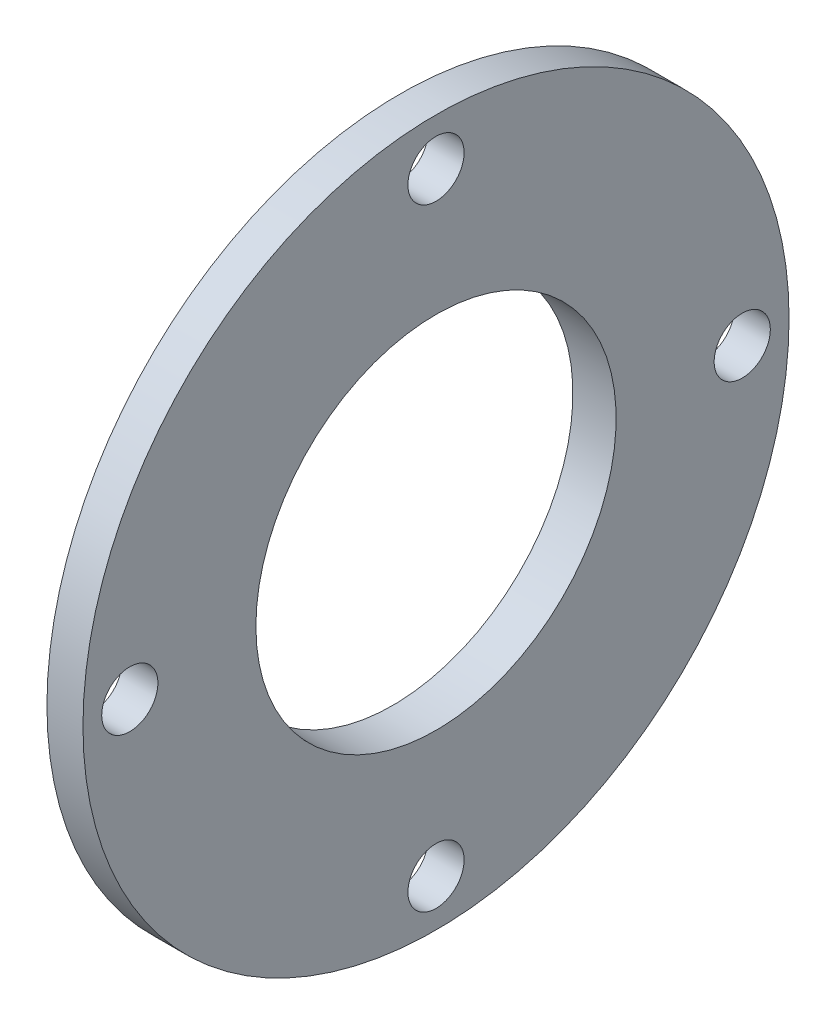
SolidWorks part; units mm, degrees
ref_plane "Front Plane" through (0, 0, 0) normal (0, 0, 1) x (1, 0, 0)
ref_plane "Top Plane" through (0, 0, 0) normal (0, 1, 0) x (1, 0, 0)
ref_plane "Right Plane" through (0, 0, 0) normal (1, 0, 0) x (0, 0, -1)
sketch "Sketch1" plane through (0, 0, 0) normal (0, 0, 1) x (1, 0, 0)
  line L0 (0, 0) -> (169.2135, 0)
  line L1 (0, 31) -> (0, 36)
  line L2 (0, 36) -> (3, 36)
  line L3 (3, 36) -> (3, 49)
  line L4 (3, 49) -> (8, 49)
  line L5 (8, 49) -> (8, 25)
  line L6 (8, 25) -> (2, 25)
  line L7 (2, 25) -> (2, 31)
  line L8 (2, 31) -> (0, 31)
  dimension "D1" = 25
  dimension "D2" = 6
  dimension "D3" = 2
  dimension "D4" = 5
  dimension "D5" = 36
  dimension "D6" = 13
  dimension "D7" = 5
revolve "Revolve1" add sketch "Sketch1" angle 360 about L0
sketch "Sketch2" plane through (0, 0, 0) normal (1, 0, 0) x (0, 0, -1)
  circle A0 centre (0, 0) radius 42.5
  circle A1 centre (42.5, 0) radius 3.9
  dimension "D1" = 85
  dimension "D2" = 7.8
extrude "Cut-Extrude1" cut sketch "Sketch2" along normal through all both and the other way through all contours A0 A1
pattern_circular "CirPattern1" count 4 over 360 about axis through (0, 0, 0) along (1, 0, 0) of "Cut-Extrude1"
